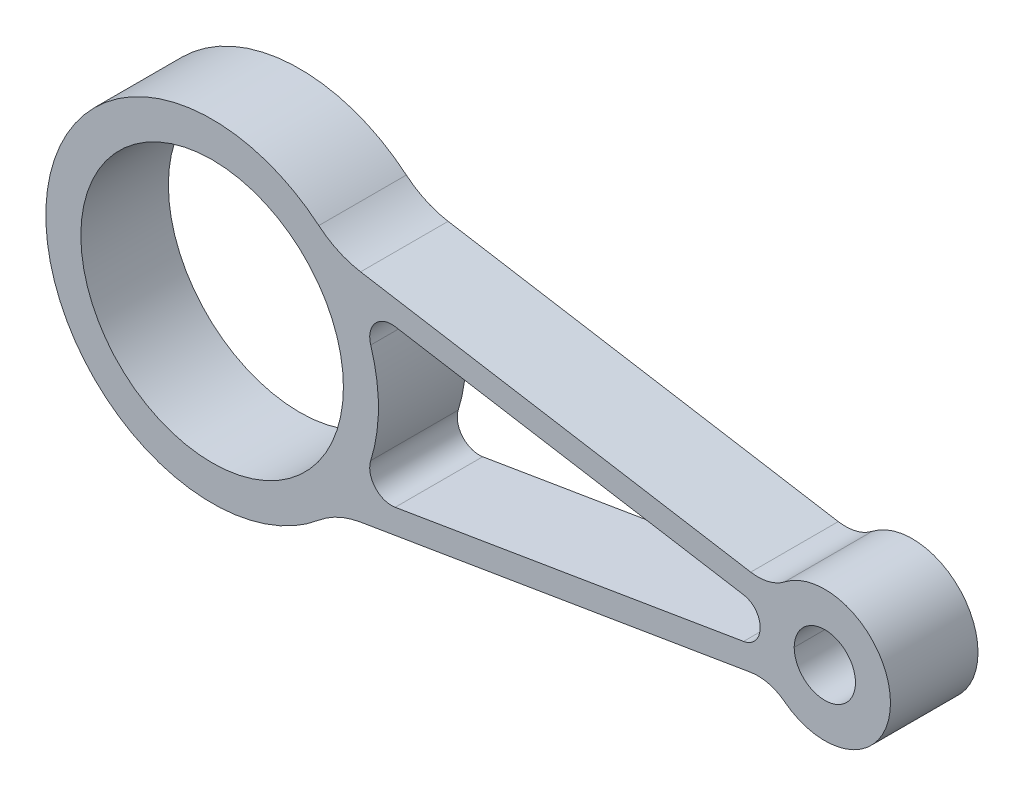
SolidWorks part; units mm, degrees
material "steel 1"
ref_plane "Front" through (0, 0, 0) normal (0, 0, 1) x (1, 0, 0)
ref_plane "Top" through (0, 0, 0) normal (0, 1, 0) x (1, 0, 0)
ref_plane "Right" through (0, 0, 0) normal (1, 0, 0) x (0, 0, -1)
sketch "Sketch1" plane through (0, 0, 0) normal (0, 0, 1) x (1, 0, 0)
  line L0 (-42.1775, 0) -> (237.8949, 0) construction
  line L1 (27.9355, 25.7606) -> (128.0638, 9.0844)
  line L2 (27.9355, -25.7606) -> (128.0638, -9.0844)
  arc A0 (27.9355, 25.7606) -> (27.9355, -25.7606) centre (0, 0) ccw
  arc A1 (128.0638, -9.0844) -> (128.0638, 9.0844) centre (140, 0) ccw
  circle A2 centre (0, 0) radius 30
  circle A3 centre (140, 0) radius 7
  dimension "D1" = 76
  dimension "D3" = 60
  dimension "D4" = 14
  dimension "D5" = 30
  dimension "D2" = 140
extrude "Base-Extrude" add sketch "Sketch1" against normal blind 20
fillet "Fillet1" radius 10 2 edges at (128.0638, 9.0844, -10) (128.0638, -9.0844, -10)
fillet "Fillet2" radius 20 2 edges at (27.9355, 25.7606, -10) (27.9355, -25.7606, -10)
sketch "Sketch2" plane through (0, 0, 0) normal (0, 0, 1) x (1, 0, 0)
  line L0 (41.8286, 17.871) -> (121.0469, 4.6773)
  line L1 (123.0688, 9.9163) -> (33.9231, 24.7634) construction
  line L2 (41.8286, -17.871) -> (121.0718, -4.6731)
  line L3 (33.9231, -24.7634) -> (123.0688, -9.9163) construction
  arc A0 (36.2389, -11.4344) -> (36.2389, 11.4344) centre (0, 0) ccw
  arc A3 (36.2389, 11.4344) -> (41.8286, 17.871) centre (41.0071, 12.9389) cw
  arc A4 (41.8286, -17.871) -> (36.2389, -11.4344) centre (41.0071, -12.9389) cw
  arc A5 (124.8077, 0.2384) -> (121.0469, 4.6773) centre (120.3077, 0.2384) ccw
  arc A6 (124.8077, 0.2384) -> (121.0718, -4.6731) centre (120.3325, -0.2343) cw
  dimension "D1" = 76
  dimension "D5" = 5
  dimension "D6" = 5
  dimension "D7" = 4.5
  dimension "D8" = 4.5
  dimension "D3" = 5.5
  dimension "D4" = 5.5
extrude "Cut-Extrude1" cut sketch "Sketch2" against normal blind 5
sketch "Sketch3" plane through (0, 0, -20) normal (0, 0, -1) x (-1, 0, 0)
  line L0 (-121.4456, 4.6109) -> (-41.8286, 17.871)
  line L1 (-123.0688, 9.9163) -> (-33.9231, 24.7634) construction
  line L2 (-121.4335, -4.6129) -> (-41.8286, -17.871)
  line L3 (-33.9231, -24.7634) -> (-123.0688, -9.9163) construction
  arc A0 (-36.2389, 11.4344) -> (-36.2389, -11.4344) centre (0, 0) ccw
  arc A1 (-41.8286, 17.871) -> (-36.2389, 11.4344) centre (-41.0071, 12.9389) cw
  arc A3 (-125.1942, -0.1579) -> (-121.4456, 4.6109) centre (-120.7063, 0.172) cw
  arc A4 (-125.1942, -0.1579) -> (-121.4335, -4.6129) centre (-120.6942, -0.174) ccw
  arc A5 (-41.8286, -17.871) -> (-36.2389, -11.4344) centre (-41.0071, -12.9389) ccw
  dimension "D1" = 76
  dimension "D2" = 5
  dimension "D5" = 4.5
  dimension "D6" = 4.5
  dimension "D7" = 5
  dimension "D3" = 5.5
  dimension "D4" = 5.5
extrude "Cut-Extrude2" cut sketch "Sketch3" against normal through all
split line "Split Line1"
